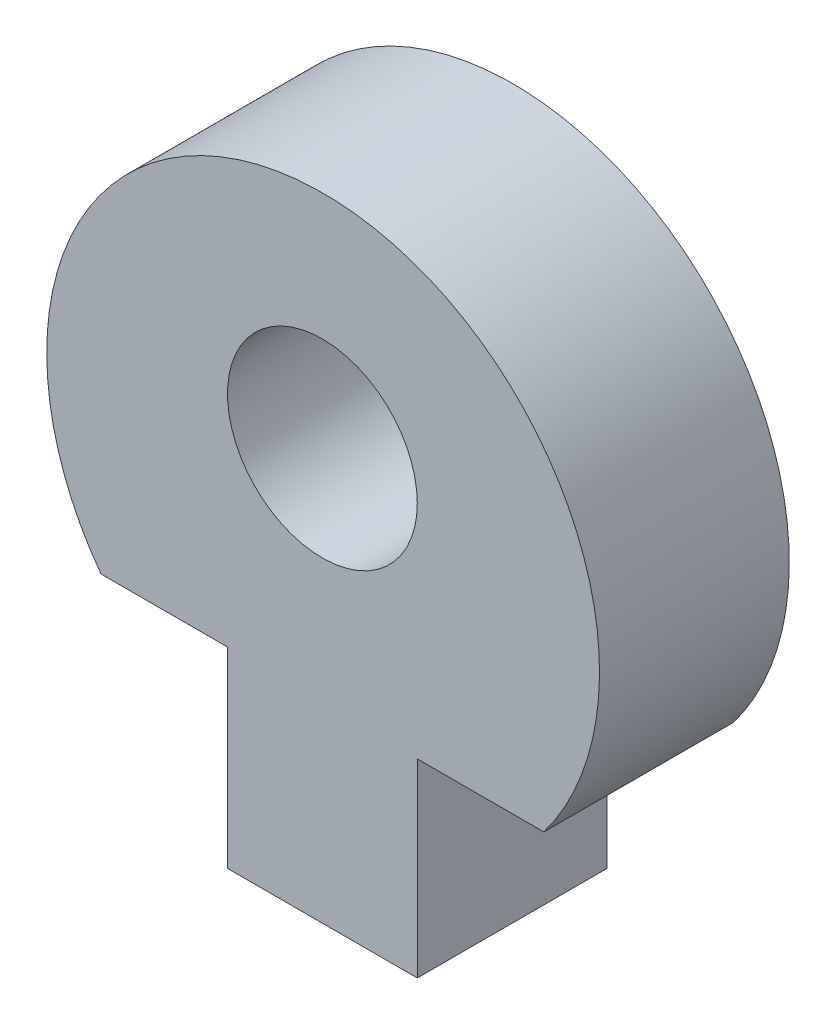
SolidWorks part; units mm, degrees
ref_plane "Front Plane" through (0, 0, 0) normal (0, 0, 1) x (1, 0, 0)
ref_plane "Top Plane" through (0, 0, 0) normal (0, 1, 0) x (1, 0, 0)
ref_plane "Right Plane" through (0, 0, 0) normal (1, 0, 0) x (0, 0, -1)
sketch "Model" plane through (0, 0, 0) normal (0, 0, 1) x (1, 0, 0)
  line L0 (55.9465, 18.4176) -> (55.9465, 12.4176)
  line L1 (55.9465, 12.4176) -> (49.9465, 12.4176)
  line L2 (55.9465, 18.4176) -> (59.9465, 18.4176)
  line L3 (45.9465, 18.4794) -> (49.9465, 18.4794)
  line L4 (49.9465, 12.4176) -> (49.9465, 18.4794)
  circle A0 centre (52.9465, 25.4176) radius 3
  arc A1 (59.9465, 18.4176) -> (45.9465, 18.4794) centre (52.9696, 23.6791) ccw
extrude "Boss-Extrude1" add sketch "Model" along normal blind 6 contours A0 | L3 L4 L1 L0 L2 A1
